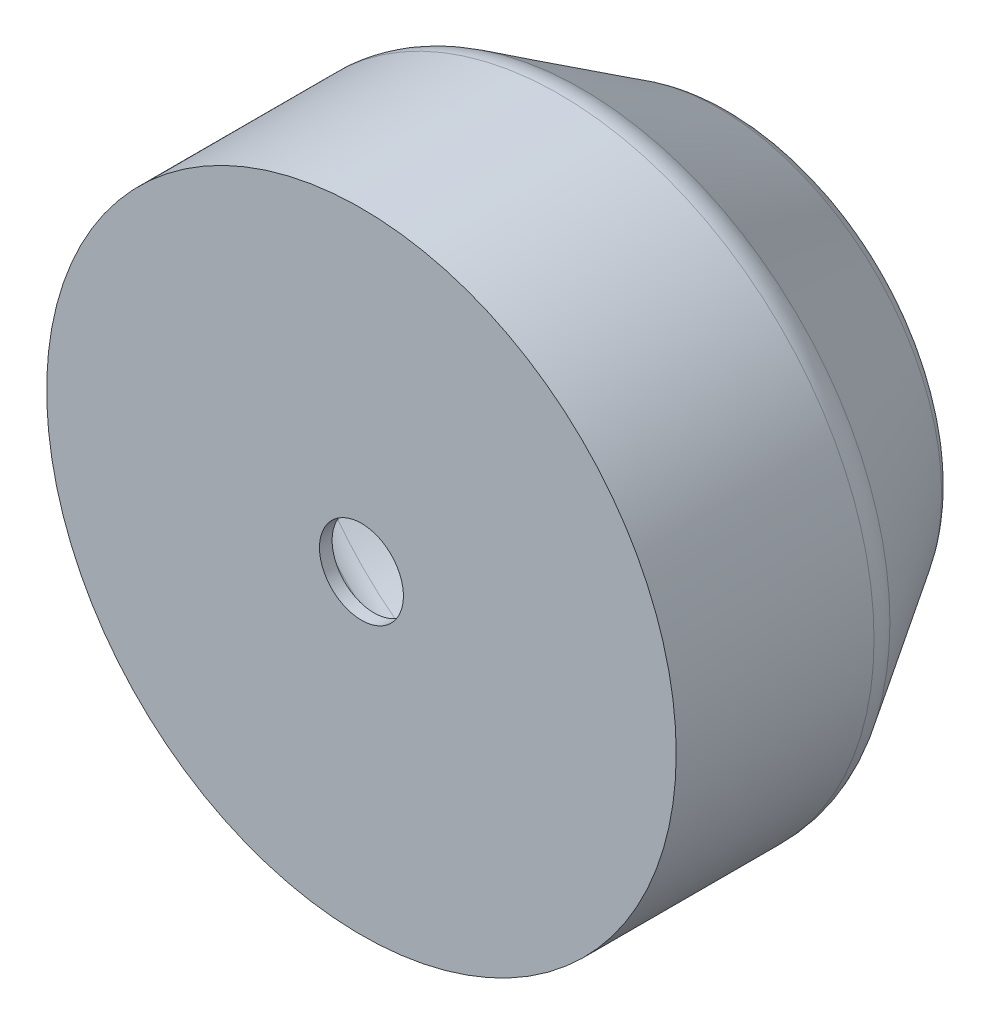
SolidWorks part; units mm, degrees
ref_plane "前视基准面" through (0, 0, 0) normal (0, 0, 1) x (1, 0, 0)
ref_plane "上视基准面" through (0, 0, 0) normal (0, 1, 0) x (1, 0, 0)
ref_plane "右视基准面" through (0, 0, 0) normal (1, 0, 0) x (0, 0, -1)
sketch "草图1" plane through (0, 0, 0) normal (0, 0, 1) x (1, 0, 0)
  circle A0 centre (0, 0) radius 75
  dimension "D1" = 150
extrude "凸台-拉伸1" add sketch "草图1" along normal blind 50
sketch "草图2" plane through (0, 0, 0) normal (0, 0, -1) x (-1, 0, 0)
  circle A1 centre (0, 0) radius 75
  circle A2 centre (0, 0) radius 75
  dimension "D1" = 0
ref_plane "基准面1" through (0, 0, -40) normal (0, 0, -1) x (-1, 0, 0)
sketch "草图3" plane through (0, 0, -40) normal (0, 0, -1) x (-1, 0, 0)
  circle A0 centre (0, 0) radius 50
  dimension "D1" = 100
loft "放样1" add profiles "草图3", "草图2"
fillet "圆角1" radius 10 2 edges at (-50, 0, -40) (-75, 0, 0)
sketch "草图4" plane through (0, 0, -40) normal (0, 0, -1) x (-1, 0, 0)
  circle A0 centre (0, 0) radius 10
  dimension "D1" = 20
extrude "切除-拉伸1" cut sketch "草图4" against normal through all
shell "抽壳1" thickness 3
